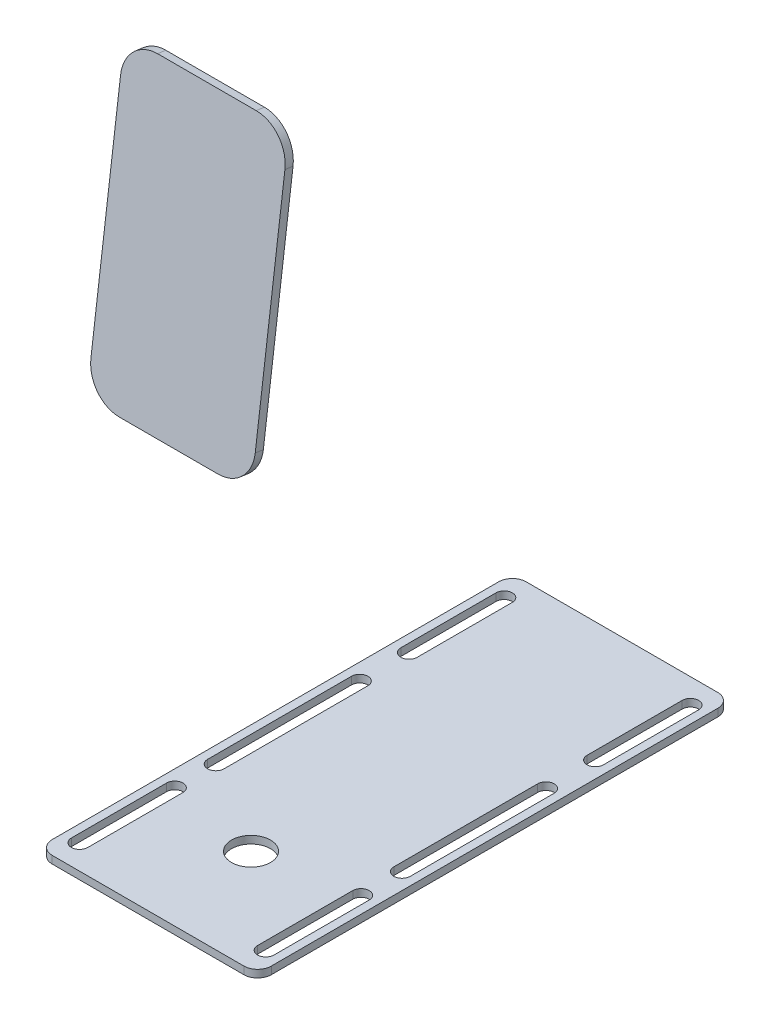
SolidWorks part; units mm, degrees
ref_plane "Front Plane" through (0, 0, 0) normal (0, 0, 1) x (1, 0, 0)
ref_plane "Top Plane" through (0, 0, 0) normal (0, 1, 0) x (1, 0, 0)
ref_plane "Right Plane" through (0, 0, 0) normal (1, 0, 0) x (0, 0, -1)
sketch "Sketch1" plane through (0, 0, 0) normal (0, 1, 0) x (1, 0, 0)
  line L0 (34, 77.5187) -> (34, 42.7687) construction
  line L1 (-35, 86.5188) -> (35, 86.5188)
  line L2 (-40, 81.5187) -> (-40, -81.5187)
  line L3 (-35, -86.5187) -> (35, -86.5187)
  line L4 (40, 81.5187) -> (40, -81.5187)
  line L5 (-40, 86.5188) -> (40, -86.5187) construction
  line L6 (-40, -86.5187) -> (40, 86.5188) construction
  line L7 (37, 77.5187) -> (37, 42.7687)
  line L8 (31, 77.5187) -> (31, 42.7687)
  line L9 (-40, 0) -> (40, 0) construction
  line L10 (0, 86.5188) -> (0, -86.5187) construction
  line L11 (-34, 77.5187) -> (-34, 42.7687) construction
  line L12 (-37, 77.5187) -> (-37, 42.7687)
  line L13 (-31, 77.5187) -> (-31, 42.7687)
  line L14 (34, -77.5187) -> (34, -42.7687) construction
  line L15 (37, -77.5187) -> (37, -42.7687)
  line L16 (31, -77.5187) -> (31, -42.7687)
  line L17 (-34, -77.5187) -> (-34, -42.7687) construction
  line L18 (-37, -77.5187) -> (-37, -42.7687)
  line L19 (-31, -77.5187) -> (-31, -42.7687)
  line L20 (34, 24.7687) -> (34, -27.7687) construction
  line L21 (37, 24.7687) -> (37, -27.7687)
  line L22 (31, 24.7687) -> (31, -27.7687)
  line L23 (-34, 24.7687) -> (-34, -27.7687) construction
  line L24 (-37, 24.7687) -> (-37, -27.7687)
  line L25 (-31, 24.7687) -> (-31, -27.7687)
  arc A0 (-40, -81.5187) -> (-35, -86.5187) centre (-35, -81.5187) ccw
  arc A1 (35, -86.5187) -> (40, -81.5187) centre (35, -81.5187) ccw
  arc A2 (35, 86.5188) -> (40, 81.5187) centre (35, 81.5187) cw
  arc A3 (-35, 86.5188) -> (-40, 81.5187) centre (-35, 81.5187) ccw
  arc A4 (37, 77.5187) -> (31, 77.5187) centre (34, 77.5187) ccw
  arc A5 (31, 42.7687) -> (37, 42.7687) centre (34, 42.7687) ccw
  arc A6 (-37, 77.5187) -> (-31, 77.5187) centre (-34, 77.5187) cw
  arc A7 (-31, 42.7687) -> (-37, 42.7687) centre (-34, 42.7687) cw
  arc A8 (37, -77.5187) -> (31, -77.5187) centre (34, -77.5187) cw
  arc A9 (31, -42.7687) -> (37, -42.7687) centre (34, -42.7687) cw
  arc A10 (-37, -77.5187) -> (-31, -77.5187) centre (-34, -77.5187) ccw
  arc A11 (-31, -42.7687) -> (-37, -42.7687) centre (-34, -42.7687) ccw
  arc A12 (37, 24.7687) -> (31, 24.7687) centre (34, 24.7687) ccw
  arc A13 (31, -27.7687) -> (37, -27.7687) centre (34, -27.7687) ccw
  arc A14 (-37, 24.7687) -> (-31, 24.7687) centre (-34, 24.7687) cw
  arc A15 (-31, -27.7687) -> (-37, -27.7687) centre (-34, -27.7687) cw
  circle A16 centre (0, -48.9201) radius 7.112
  point P0 (0, 0)
  point P20 (34, 60.1437)
  point P31 (-34, 60.1437)
  point P38 (34, -60.1437)
  point P45 (-34, -60.1437)
  point P52 (34, -1.5)
  point P59 (-34, -1.5)
  dimension "D3" = 5
  dimension "D6" = 6
  dimension "D5" = 40.75
  dimension "D9" = 12
  dimension "D10" = 9
  dimension "D1" = 80
  dimension "D2" = 173.0375
  dimension "D4" = 3
  dimension "D7" = 6
  dimension "D8" = 6
extrude "Boss-Extrude1" add sketch "Sketch1" along normal blind 2.75
sketch "Sketch2" plane through (0, 0, 0) normal (1, 0, 0) x (0, 0, -1)
  line L0 (-65.0187, 254) -> (-78.9187, 146)
  line L1 (-86.5187, 89.4829) -> (-86.5187, 186.7974) construction
  line L2 (-81.5187, 0) -> (81.5187, 0) construction
  dimension "D1" = 7.6
  dimension "D2" = 21.5
  dimension "D3" = 146
  dimension "D4" = 254
  dimension "D5" = 82.666
ref_plane "Plane1" through (0, 12.3707, 96.1173) normal (0, 0.1277, 0.9918) x (0, -0.9918, 0.1277)
sketch "Sketch3" plane through (0, 12.3707, 96.1173) normal (0, 0.1277, 0.9918) x (0, -0.9918, 0.1277)
  line L0 (-243.6224, 0) -> (-134.7316, 0) construction
  line L1 (-231.6224, 30) -> (-146.7316, 30)
  line L2 (-243.6224, 18) -> (-243.6224, -18)
  line L3 (-231.6224, -30) -> (-146.7316, -30)
  line L4 (-134.7316, 18) -> (-134.7316, -18)
  line L5 (-243.6224, 0) -> (-134.7316, 0) construction
  arc A0 (-231.6224, 30) -> (-243.6224, 18) centre (-231.6224, 18) ccw
  arc A1 (-243.6224, -18) -> (-231.6224, -30) centre (-231.6224, -18) ccw
  arc A2 (-146.7316, -30) -> (-134.7316, -18) centre (-146.7316, -18) ccw
  arc A3 (-146.7316, 30) -> (-134.7316, 18) centre (-146.7316, 18) cw
  point P6 (-243.6224, 0)
  point P7 (-134.7316, 0)
  dimension "D2" = 12
  dimension "D1" = 60
extrude "Boss-Extrude2" add sketch "Sketch3" against normal blind 3 separate body
